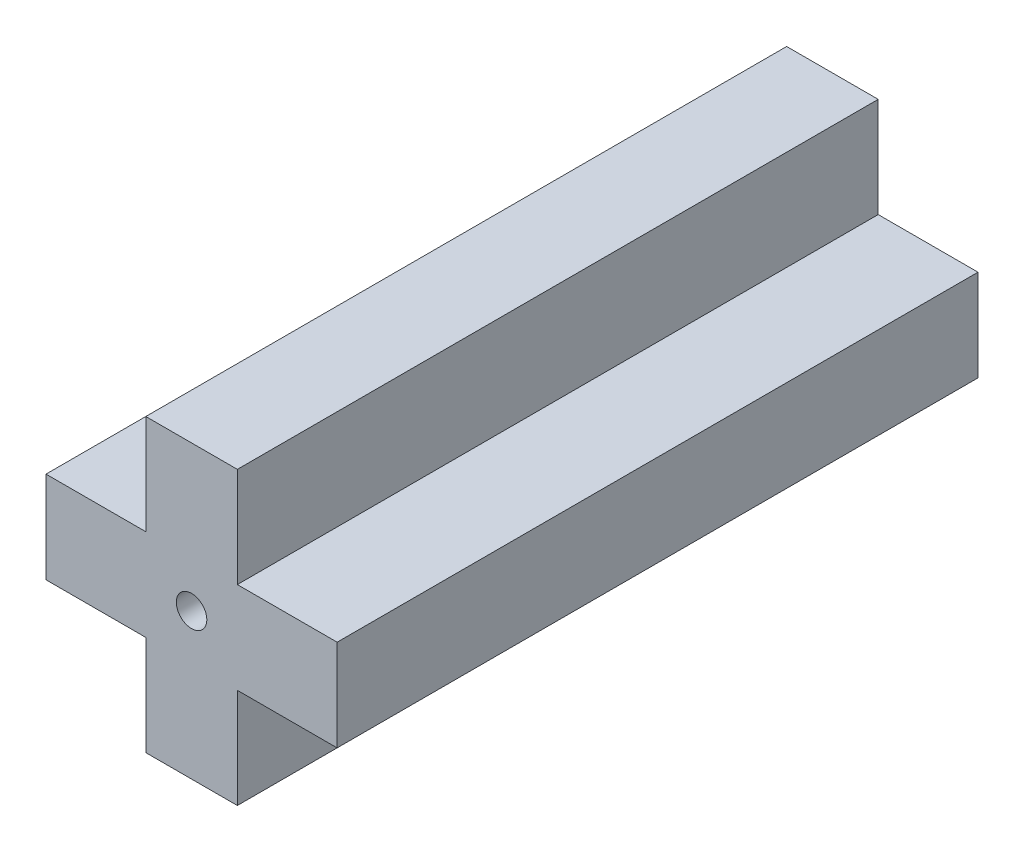
SolidWorks part; units mm, degrees
ref_plane "Front Plane" through (0, 0, 0) normal (0, 0, 1) x (1, 0, 0)
ref_plane "Top Plane" through (0, 0, 0) normal (0, 1, 0) x (1, 0, 0)
ref_plane "Right Plane" through (0, 0, 0) normal (1, 0, 0) x (0, 0, -1)
sketch "Sketch2" plane through (0, 0, 0) normal (0, 0, 1) x (1, 0, 0)
  line L0 (1.5, 0) -> (4.77, 0)
  line L1 (4.77, 0) -> (4.77, 3)
  line L2 (4.77, 3) -> (1.5, 3)
  line L3 (1.5, 3) -> (1.5, 6.27)
  line L4 (1.5, 6.27) -> (-1.5, 6.27)
  line L5 (-1.5, 6.27) -> (-1.5, 3)
  line L6 (-1.5, 3) -> (-4.77, 3)
  line L7 (-4.77, 3) -> (-4.77, 0)
  line L8 (-4.77, 0) -> (-1.5, 0)
  line L9 (-1.5, 0) -> (-1.5, -3.27)
  line L10 (-1.5, -3.27) -> (1.5, -3.27)
  line L11 (1.5, -3.27) -> (1.5, 0)
  circle A0 centre (0, 1.5) radius 0.5
  point P11 (0, 0)
  point P14 (4.77, 1.5)
  point P15 (0, 6.27)
  dimension "D1" = 1
  dimension "D2" = 9.54
  dimension "D3" = 3
  dimension "D4" = 3.27
  dimension "D5" = 3.27
  dimension "D6" = 3
  dimension "D7" = 3.27
  dimension "D8" = 3.27
  dimension "D9" = 3
extrude "Boss-Extrude1" add sketch "Sketch2" along normal blind 21
